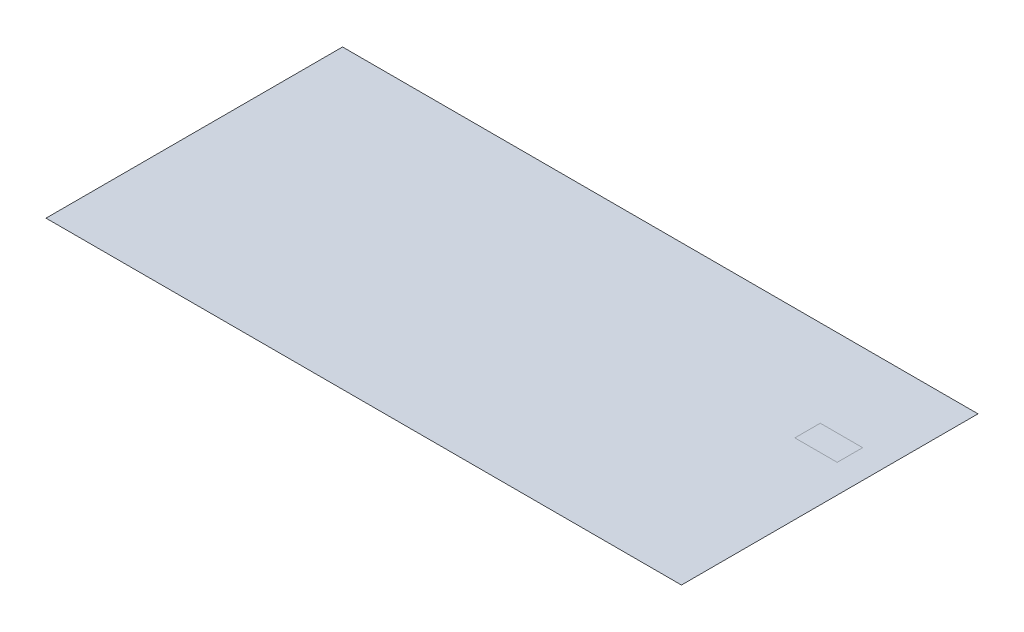
SolidWorks part; units mm, degrees
ref_plane "Front Plane" through (0, 0, 0) normal (0, 0, 1) x (1, 0, 0)
ref_plane "Top Plane" through (0, 0, 0) normal (0, 1, 0) x (1, 0, 0)
ref_plane "Right Plane" through (0, 0, 0) normal (1, 0, 0) x (0, 0, -1)
sketch "Sketch1" plane through (0, 0, 0) normal (0, 1, 0) x (1, 0, 0)
  line L0 (0, 0) -> (0, -7000)
  line L1 (0, 0) -> (15000, 0)
  line L2 (15000, 0) -> (15000, -7000)
  line L3 (15000, -7000) -> (0, -7000)
extrude "Boss-Extrude2" add sketch "Sketch1" against normal blind 0.001
sketch "Sketch2" plane through (0, 0, 0) normal (0, 1, 0) x (1, 0, 0)
  line L4 (14330, -2053) -> (14330, -2653)
  line L5 (14330, -2053) -> (13330, -2053)
  line L6 (14330, -2653) -> (13330, -2653)
  line L7 (13330, -2653) -> (13330, -2053)
split line "Split Line1"
